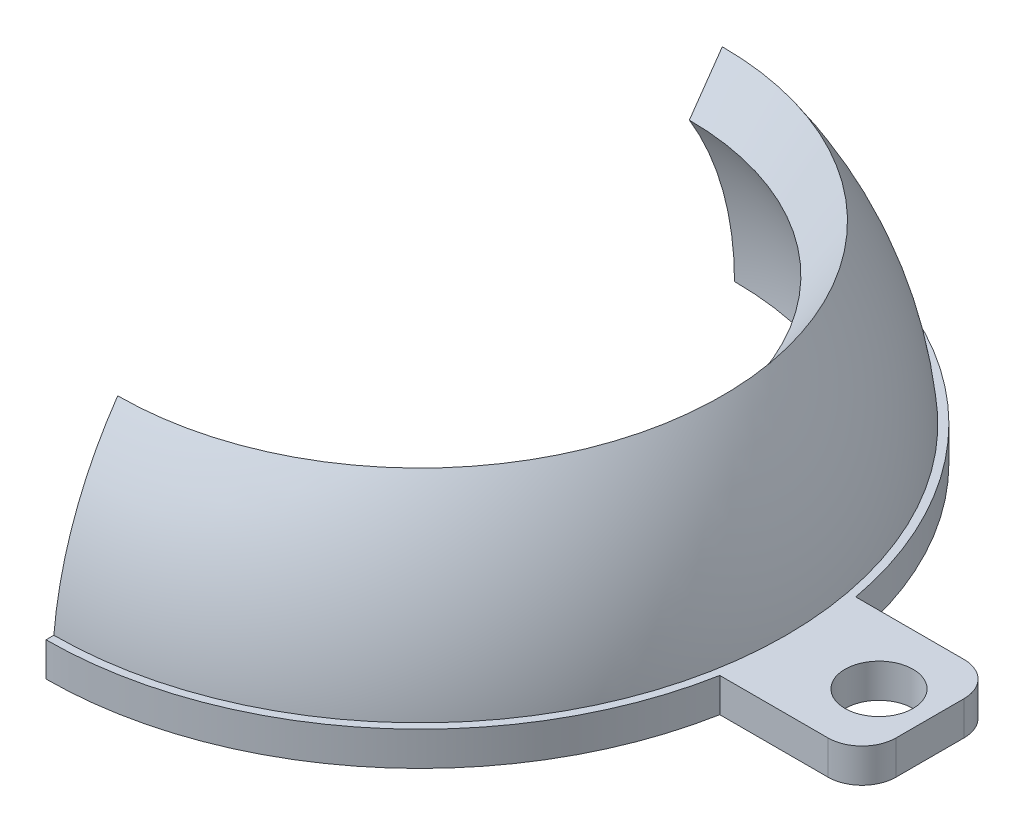
SolidWorks part; units mm, degrees
other "Markup1"
sketch "Sketch6" plane through (0, 12.3201, -22) normal (-0.0161, 0.8638, -0.5037) x (-0.9993, 0.0034, 0.0378)
ref_plane "Front Plane" through (0, 0, 0) normal (0, 0, 1) x (1, 0, 0)
ref_plane "Top Plane" through (0, 0, 0) normal (0, 1, 0) x (1, 0, 0)
ref_plane "Right Plane" through (0, 0, 0) normal (1, 0, 0) x (0, 0, -1)
sketch "Sketch2" plane through (0, 0, 0) normal (0, 1, 0) x (1, 0, 0)
  line L0 (28, 4) -> (-28, 4)
  line L1 (30, 2) -> (30, -2)
  line L2 (28, -4) -> (-28, -4)
  line L3 (-30, 2) -> (-30, -2)
  line L4 (30, 4) -> (-30, -4) construction
  line L5 (30, -4) -> (-30, 4) construction
  circle A0 centre (0, 0) radius 18.5
  circle A1 centre (0, 0) radius 22
  circle A2 centre (27, 0) radius 2
  circle A3 centre (-27, 0) radius 2
  arc A4 (-28, 4) -> (-30, 2) centre (-28, 2) ccw
  arc A5 (-28, -4) -> (-30, -2) centre (-28, -2) cw
  arc A6 (30, -2) -> (28, -4) centre (28, -2) cw
  arc A7 (28, 4) -> (30, 2) centre (28, 2) cw
  point P0 (0, 0)
  dimension "D3" = 4
  dimension "D5" = 2
  dimension "D6" = 37
  dimension "D8" = 4
  dimension "D1" = 60
  dimension "D2" = 8
  dimension "D4" = 3
  dimension "D7" = 3
  dimension "D9" = 3.5
extrude "Boss-Extrude1" add sketch "Sketch2" along normal blind 2 contours L2 A0 | A5 L2 A0 L0 A4 L3 A3 | L0 A0 | L2 A0 L0 | A7 L0 A0 L2 A6 L1 A2 | A1
sketch "Sketch4" plane through (0, 0, 0) normal (0, 0, 1) x (1, 0, 0)
  line L0 (-18.5, 0) -> (18.5, 0) construction
  line L1 (-21.6333, 0) -> (21.6333, 0) construction
  line L2 (-18.5, 0) -> (18.5, 0)
  line L3 (-21.6333, 0) -> (21.6333, 0)
  line L4 (0, 21.6333) -> (0, 0) construction
  line L5 (0, 0) -> (-12.4084, 17.721) construction
  line L6 (-9.1558, 0) -> (-17.7824, 12.3201)
  arc A0 (-21.6333, 0) -> (0, 21.6333) centre (0, 0) cw
  arc A1 (-18.5, 0) -> (0, 18.5) centre (0, 0) cw
  dimension "D1" = 55
  dimension "D2" = 7.5
revolve "Revolve1" add sketch "Sketch4" angle 360 about L4
sketch "Sketch5" plane through (0, 0, 0) normal (1, 0, 0) x (0, 0, -1)
  line L1 (34.349, -17.6355) -> (-34.349, -17.6355)
  line L2 (34.349, -17.6355) -> (34.349, 17.6355)
  line L3 (34.349, 17.6355) -> (-34.349, 17.6355)
  line L4 (-34.349, -17.6355) -> (-34.349, 17.6355)
  line L5 (34.349, -17.6355) -> (-34.349, 17.6355) construction
  line L6 (34.349, 17.6355) -> (-34.349, -17.6355) construction
  point P0 (0, 0)
extrude "Cut-Extrude1" cut sketch "Sketch5" against normal through all
